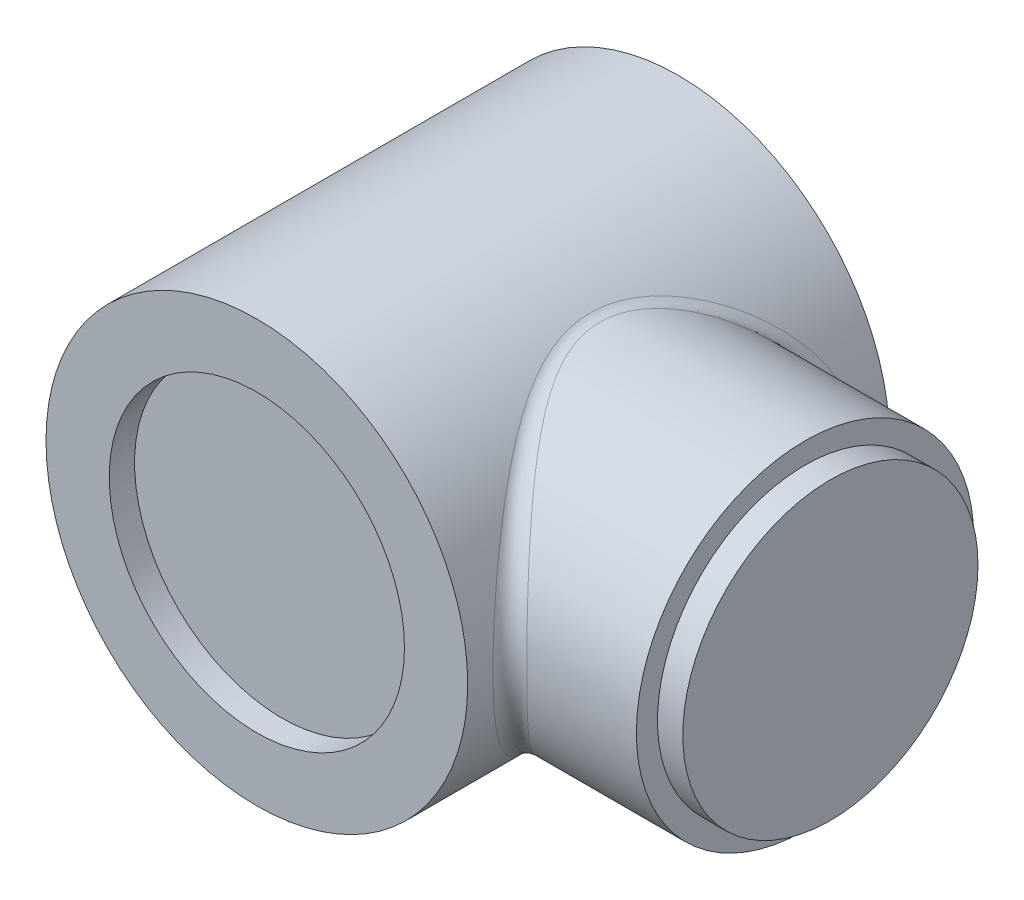
SolidWorks part; units mm, degrees
ref_plane "Front Plane" through (0, 0, 0) normal (0, 0, 1) x (1, 0, 0)
ref_plane "Top Plane" through (0, 0, 0) normal (0, 1, 0) x (1, 0, 0)
ref_plane "Right Plane" through (0, 0, 0) normal (1, 0, 0) x (0, 0, -1)
sketch "Sketch1" plane through (0, 0, 0) normal (0, 0, 1) x (1, 0, 0)
  circle A0 centre (0, 0) radius 25
  dimension "D1" = 50
extrude "Boss-Extrude1" add sketch "Sketch1" along normal mid plane 50
sketch "Sketch2" plane through (0, 0, 25) normal (0, 0, 1) x (1, 0, 0)
  circle A0 centre (0, 0) radius 17.5
  dimension "D1" = 35
extrude "Cut-Extrude1" cut sketch "Sketch2" against normal blind 3
mirror "Mirror1" about plane through (0, 0, 0) normal (0, 0, 1) of "Cut-Extrude1"
sketch "Sketch3" plane through (0, 0, 0) normal (1, 0, 0) x (0, 0, -1)
  circle A0 centre (0, 0) radius 20
  dimension "D1" = 40
extrude "Boss-Extrude2" add sketch "Sketch3" along normal blind 40
sketch "Sketch4" plane through (40, 0, 0) normal (1, 0, 0) x (0, 0, -1)
  circle A0 centre (0, 0) radius 17.5
  dimension "D1" = 35
extrude "Boss-Extrude3" add sketch "Sketch4" along normal blind 3
fillet "Fillet1" radius 2 1 edges at (24.89, 2.3429, -19.8623)
